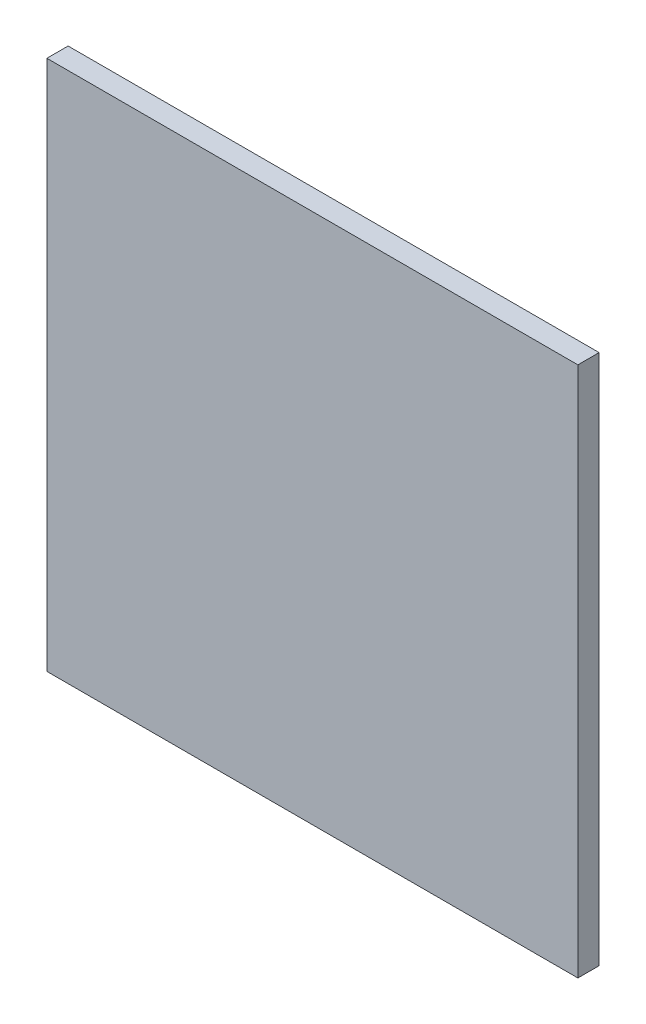
SolidWorks part; units mm, degrees
ref_plane "Front Plane" through (0, 0, 0) normal (0, 0, 1) x (1, 0, 0)
ref_plane "Top Plane" through (0, 0, 0) normal (0, 1, 0) x (1, 0, 0)
ref_plane "Right Plane" through (0, 0, 0) normal (1, 0, 0) x (0, 0, -1)
sketch "Sketch1" plane through (0, 0, 0) normal (0, 0, 1) x (1, 0, 0)
  line L1 (-12.5, 12.5) -> (12.5, 12.5)
  line L2 (-12.5, 12.5) -> (-12.5, -12.5)
  line L3 (-12.5, -12.5) -> (12.5, -12.5)
  line L4 (12.5, 12.5) -> (12.5, -12.5)
  line L5 (-12.5, 12.5) -> (12.5, -12.5) construction
  line L6 (-12.5, -12.5) -> (12.5, 12.5) construction
  point P0 (0, 0)
  dimension "D1" = 25
  dimension "D2" = 25
extrude "Boss-Extrude1" add sketch "Sketch1" along normal blind 1
